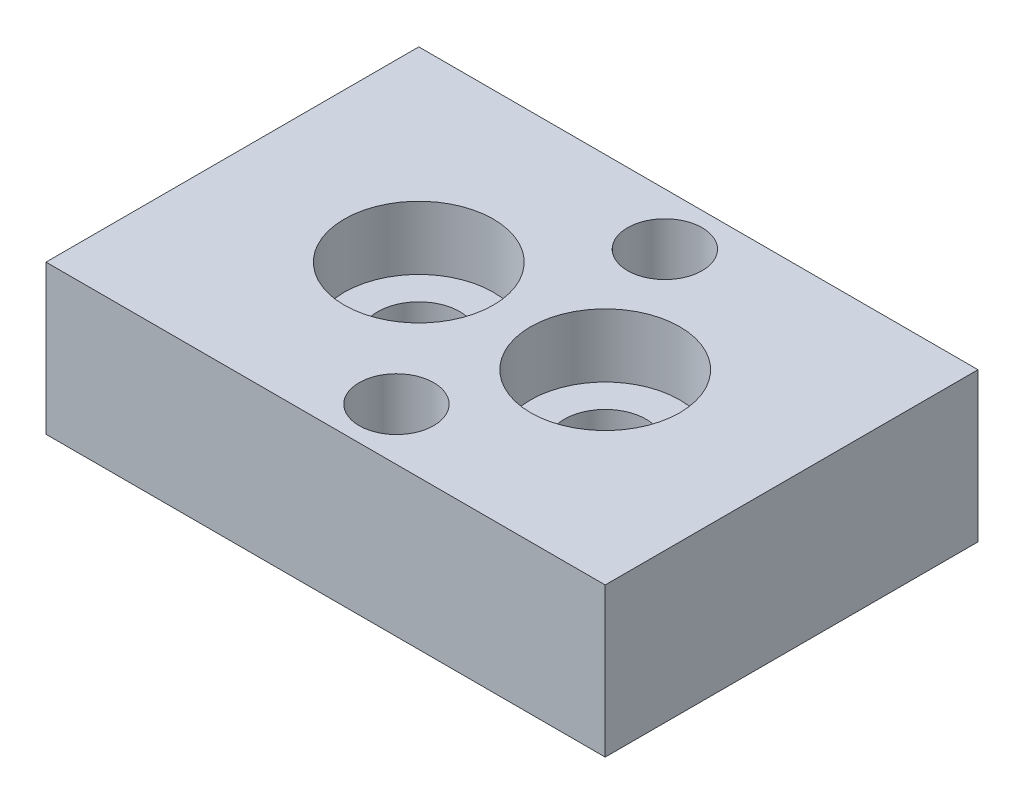
SolidWorks part; units mm, degrees
ref_plane "前视基准面" through (0, 0, 0) normal (0, 0, 1) x (1, 0, 0)
ref_plane "上视基准面" through (0, 0, 0) normal (0, 1, 0) x (1, 0, 0)
ref_plane "右视基准面" through (0, 0, 0) normal (1, 0, 0) x (0, 0, -1)
sketch "草图1" plane through (0, 0, 0) normal (0, 1, 0) x (1, 0, 0)
  line L1 (0, 0) -> (15, 0)
  line L2 (0, 0) -> (0, 10)
  line L3 (0, 10) -> (15, 10)
  line L4 (15, 0) -> (15, 10)
  dimension "D1" = 15
  dimension "D2" = 10
extrude "凸台-拉伸1" add sketch "草图1" along normal blind 4
sketch "草图2" plane through (0, 4, 0) normal (0, 1, 0) x (1, 0, 0)
  line L0 (5, 5) -> (0, 5) construction
  line L1 (0, 10) -> (0, 0) construction
  line L2 (10, 5) -> (15, 5) construction
  line L3 (15, 0) -> (15, 10) construction
  circle A0 centre (5, 5) radius 1.1
  circle A1 centre (10, 5) radius 1.1
  dimension "D1" = 2.2
  dimension "D2" = 5
extrude "切除-拉伸1" cut sketch "草图2" against normal through all
sketch "草图3" plane through (0, 4, 0) normal (0, 1, 0) x (1, 0, 0)
  circle A0 centre (5, 5) radius 2
  circle A1 centre (10, 5) radius 2
  dimension "D1" = 4
sketch "草图5" plane through (0, 4, 0) normal (0, 1, 0) x (1, 0, 0)
  line L0 (8, 1.4) -> (8, 0) construction
  line L2 (0, 0) -> (15, 0) construction
  line L4 (8, 8.6) -> (8, 10) construction
  line L5 (15, 10) -> (0, 10) construction
  line L6 (15, 0) -> (15, 10) construction
  circle A0 centre (8, 8.6) radius 1
  circle A1 centre (8, 1.4) radius 1
  dimension "D1" = 2
  dimension "D2" = 1.4
  dimension "D3" = 7
extrude "切除-拉伸4" cut sketch "草图5" against normal blind 3
extrude "切除-拉伸5" cut sketch "草图3" against normal blind 1.7
